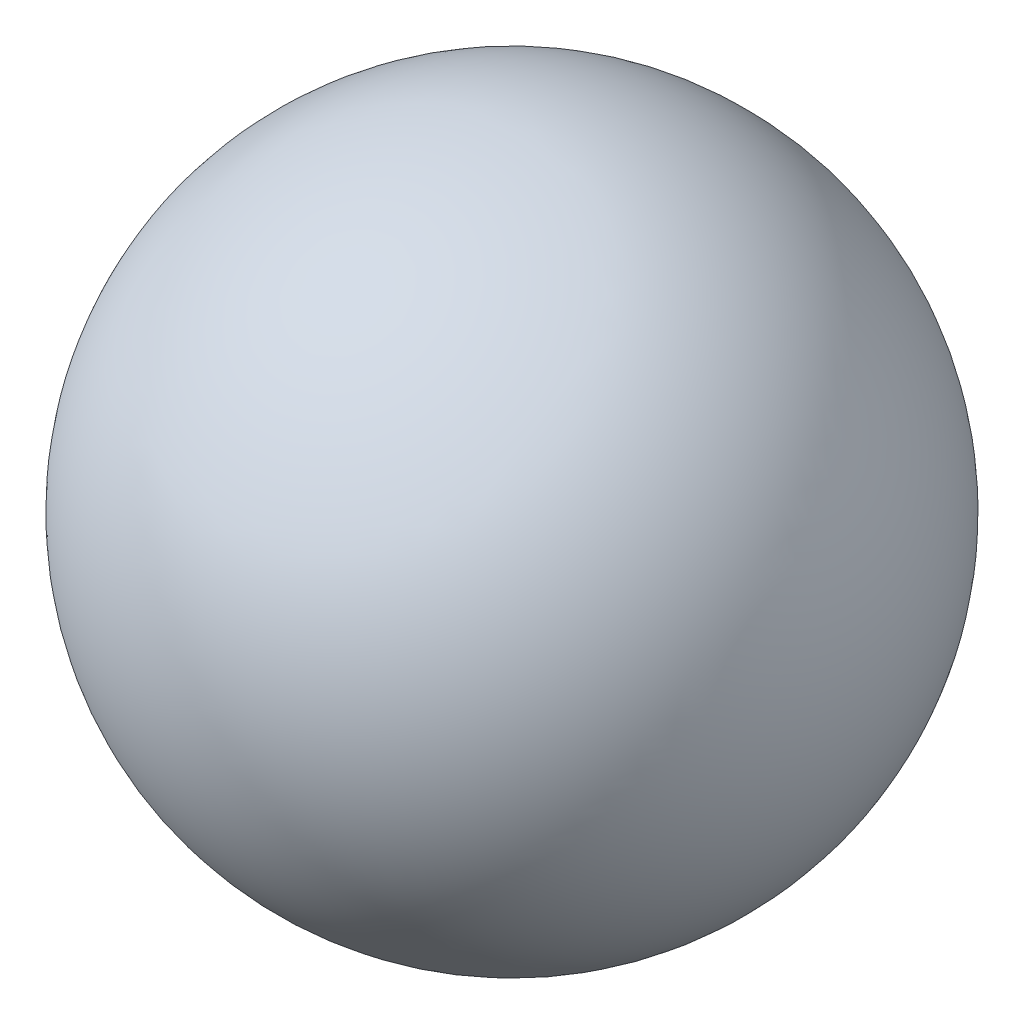
SolidWorks part; units mm, degrees
ref_plane "Front Plane" through (0, 0, 0) normal (0, 0, 1) x (1, 0, 0)
ref_plane "Top Plane" through (0, 0, 0) normal (0, 1, 0) x (1, 0, 0)
ref_plane "Right Plane" through (0, 0, 0) normal (1, 0, 0) x (0, 0, -1)
sketch "Sketch1" plane through (0, 0, 0) normal (0, 0, 1) x (1, 0, 0)
  line L0 (-5.4747, 0) -> (5.7904, 0) construction
  line L1 (-1.9845, 0) -> (1.9845, 0)
  arc A0 (1.9845, 0) -> (-1.9845, 0) centre (0, 0) ccw
  dimension "Ball Bearing" = 3.969
revolve "Revolve3" add sketch "Sketch1" angle 360 about L0
equation "\"Motor Width\"= 42.3'eg: For stepper motor Nema 17 = 42.3mm"
equation "\"Motor Hole Config Width\"= 31'eg: For stepper motor Nema 17 = 31"
equation "\"Mounting Hole Diameter\"= 3'eg: For Nema 17 3mm"
equation "\"Motor Depth\"= 50'eg: For Nema 17 50mm"
equation "\"Exposed Shaft Length\"= 22'eg: For Nema 17 22mm"
equation "\"Shaft Seround Depthr\"= 2'eg: For Nema 17 2mm"
equation "\"Shaft Diameter\"= 5'eg: For Nema 17 5mm"
equation "\"Top/Bottom Casing Depth\"= 10'Guess"
equation "\"Mid Casing Depth\"= \"Motor Depth\" - 2 * ( \"Top/Bottom Casing Depth\" )"
equation "\"Bearing Outter Diameter\"= 22' From Spec 608z = 22mm"
equation "\"Shaft Clearance Hole\"= \"Shaft Diameter\"+1.5'Guess"
equation "\"Bearing Ball Size\"= 3.969'From Spec"
equation "\"Bearing Inner Case Inner Diameter\"= 8'From Spec"
equation "\"Bearing Inner Case Outter Diameter\"= 12.1'From Spec"
equation "\"Bearing Outter Case Inner Diameter\"= 19.2'From Spec"
equation "\"Bearing Width\"= 7'From Spec"
equation "\"Ball Bearing@Sketch1\"=\"Bearing Ball Size\""
